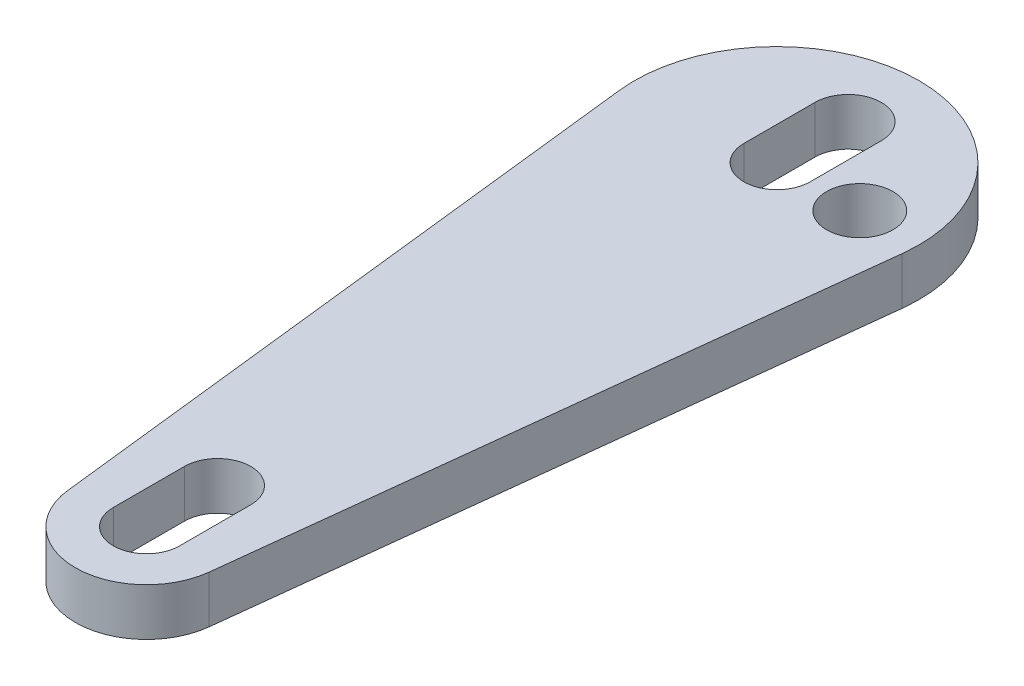
SolidWorks part; units mm, degrees
ref_plane "Front Plane" through (0, 0, 0) normal (0, 0, 1) x (1, 0, 0)
ref_plane "Top Plane" through (0, 0, 0) normal (0, 1, 0) x (1, 0, 0)
ref_plane "Right Plane" through (0, 0, 0) normal (1, 0, 0) x (0, 0, -1)
sketch "Sketch1" plane through (0, 0, 0) normal (0, 1, 0) x (1, 0, 0)
  line L0 (0, 26.58) -> (0, 0) construction
  line L3 (-5.9617, 25.9028) -> (-2.9808, -0.3386)
  line L6 (5.9617, 25.9028) -> (2.9808, -0.3386)
  line L9 (0, 0) -> (0, 3) construction
  line L12 (-1.4, 0) -> (-1.4, 3)
  line L13 (1.4, 0) -> (1.4, 3)
  line L14 (0, 29.59) -> (0, 26.59) construction
  line L15 (1.4, 29.59) -> (1.4, 26.59)
  line L16 (-1.4, 29.59) -> (-1.4, 26.59)
  circle A11 centre (0, 0) radius 1.4 construction
  arc A12 (-2.9808, -0.3386) -> (2.9808, -0.3386) centre (0, 0) ccw
  arc A13 (5.9617, 25.9028) -> (-5.9617, 25.9028) centre (0, 26.58) ccw
  circle A14 centre (0, 29.59) radius 1.4 construction
  circle A15 centre (3.5, 26.58) radius 1.4
  arc A16 (-1.4, 0) -> (1.4, 0) centre (0, 0) ccw
  arc A17 (1.4, 3) -> (-1.4, 3) centre (0, 3) ccw
  arc A18 (1.4, 29.59) -> (-1.4, 29.59) centre (0, 29.59) ccw
  arc A19 (-1.4, 26.59) -> (1.4, 26.59) centre (0, 26.59) ccw
  point P3 (0, 1.5)
  point P18 (0, 28.09)
  dimension "D1" = 2.8
  dimension "D2" = 12
  dimension "D3" = 6
  dimension "D4" = 2.8
  dimension "D5" = 26.58
  dimension "D6" = 3.01
  dimension "D7" = 3.5
  dimension "D8" = 3
  dimension "D9" = 3
extrude "Boss-Extrude1" add sketch "Sketch1" along normal blind 2
equation "\"D9@Sketch1\"=\"D8@Sketch1\""
